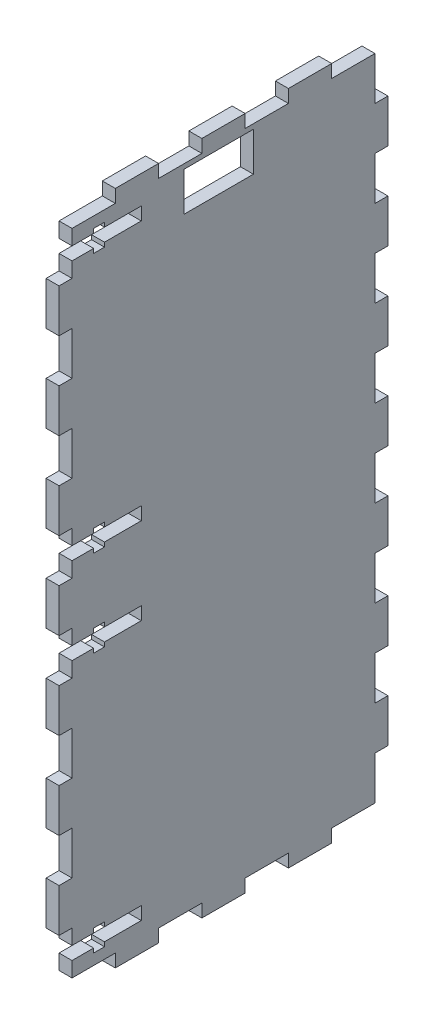
SolidWorks part; units mm, degrees
ref_plane "Front Plane" through (0, 0, 0) normal (0, 0, 1) x (1, 0, 0)
ref_plane "Top Plane" through (0, 0, 0) normal (0, 1, 0) x (1, 0, 0)
ref_plane "Right Plane" through (0, 0, 0) normal (1, 0, 0) x (0, 0, -1)
sketch "Sketch1" plane through (0, 0, 0) normal (1, 0, 0) x (0, 0, -1)
  line L0 (41.909, 148.8936) -> (25.909, 148.8936)
  line L1 (10, 153.0059) -> (20, 153.0059)
  line L2 (0, 140) -> (0, 143.5)
  line L3 (0, 150.0059) -> (10, 150.0059)
  line L4 (10, 150.0059) -> (10, 153.0059)
  line L5 (-3, 120) -> (0, 120)
  line L6 (-3, 130) -> (-3, 140)
  line L7 (0, 130) -> (-3, 130)
  line L8 (0, 120) -> (0, 130)
  line L9 (-3, 100) -> (0, 100)
  line L10 (-3, 110) -> (-3, 120)
  line L11 (0, 110) -> (-3, 110)
  line L12 (-3, 140) -> (0, 140)
  line L13 (0, 100) -> (0, 110)
  line L14 (-3, 80) -> (0, 80)
  line L15 (-3, 90) -> (-3, 100)
  line L16 (0, 90) -> (-3, 90)
  line L17 (0, 80) -> (0, 83.5)
  line L18 (-3, 60) -> (0, 60)
  line L19 (-3, 70) -> (-3, 80)
  line L20 (0, 70) -> (-3, 70)
  line L21 (0, 60) -> (0, 63.5)
  line L22 (-3, 40) -> (0, 40)
  line L23 (-3, 50) -> (-3, 60)
  line L24 (0, 50) -> (-3, 50)
  line L25 (0, 40) -> (0, 50)
  line L26 (-3, 20) -> (0, 20)
  line L27 (-3, 30) -> (-3, 40)
  line L28 (0, 30) -> (-3, 30)
  line L29 (0, 20) -> (0, 30)
  line L30 (-3, 10) -> (-3, 20)
  line L31 (20, 153.0059) -> (20, 150.0059)
  line L32 (0, 10) -> (-3, 10)
  line L33 (0, 0) -> (0, 3.5)
  line L34 (20, 150.0059) -> (30, 150.0059)
  line L35 (30, 153.0059) -> (40, 153.0059)
  line L36 (30, 150.0059) -> (30, 153.0059)
  line L37 (40, 153.0059) -> (40, 150.0059)
  line L38 (40, 150.0059) -> (50, 150.0059)
  line L39 (50, 153.0059) -> (60, 153.0059)
  line L40 (50, 150.0059) -> (50, 153.0059)
  line L41 (60, 153.0059) -> (60, 150.0059)
  line L42 (60, 150.0059) -> (70, 150.0059)
  line L43 (41.909, 148.8936) -> (41.909, 139.8936)
  line L44 (41.909, 139.8936) -> (25.909, 139.8936)
  line L45 (25.909, 139.8936) -> (25.909, 148.8936)
  line L46 (0, 10) -> (0, 6.5)
  line L47 (7.5, 6.5) -> (16, 6.5)
  line L48 (16, 3.5) -> (7.5, 3.5)
  line L49 (70, 0) -> (70, 3.5)
  line L50 (70, 10) -> (73, 10)
  line L51 (73, 10) -> (73, 20)
  line L52 (70, 20) -> (70, 30)
  line L53 (70, 30) -> (73, 30)
  line L54 (73, 30) -> (73, 40)
  line L55 (73, 20) -> (70, 20)
  line L56 (70, 40) -> (70, 50)
  line L57 (70, 50) -> (73, 50)
  line L58 (73, 50) -> (73, 60)
  line L59 (73, 40) -> (70, 40)
  line L60 (70, 60) -> (70, 63.5)
  line L61 (70, 70) -> (73, 70)
  line L62 (73, 70) -> (73, 80)
  line L63 (73, 60) -> (70, 60)
  line L64 (70, 80) -> (70, 83.5)
  line L65 (70, 90) -> (73, 90)
  line L66 (73, 90) -> (73, 100)
  line L67 (73, 80) -> (70, 80)
  line L68 (70, 100) -> (70, 110)
  line L69 (73, 140) -> (70, 140)
  line L70 (70, 110) -> (73, 110)
  line L71 (73, 110) -> (73, 120)
  line L72 (73, 100) -> (70, 100)
  line L73 (70, 120) -> (70, 130)
  line L74 (70, 130) -> (73, 130)
  line L75 (73, 130) -> (73, 140)
  line L76 (73, 120) -> (70, 120)
  line L77 (70, 140) -> (70, 143.5)
  line L78 (7.5, 2.5) -> (5, 2.5)
  line L79 (0, 6.5) -> (5, 6.5)
  line L80 (60, 0) -> (70, 0)
  line L81 (60, -3) -> (60, 0)
  line L82 (50, 0) -> (50, -3)
  line L83 (50, -3) -> (60, -3)
  line L84 (40, 0) -> (50, 0)
  line L85 (40, -3) -> (40, 0)
  line L86 (30, 0) -> (30, -3)
  line L87 (30, -3) -> (40, -3)
  line L88 (20, 0) -> (30, 0)
  line L89 (20, -3) -> (20, 0)
  line L90 (10, 0) -> (10, -3)
  line L91 (0, 0) -> (10, 0)
  line L92 (10, -3) -> (20, -3)
  line L93 (16, 6.5) -> (16, 3.5)
  line L94 (7.5, 2.5) -> (7.5, 3.5)
  line L95 (7.5, 7.5) -> (5, 7.5)
  line L96 (5, 2.5) -> (5, 3.5)
  line L97 (5, 6.5) -> (5, 7.5)
  line L98 (7.5, 6.5) -> (7.5, 7.5)
  line L99 (5, 3.5) -> (0, 3.5)
  line L100 (5, 63.5) -> (0, 63.5)
  line L101 (0, 66.5) -> (5, 66.5)
  line L102 (7.5, 66.5) -> (16, 66.5)
  line L103 (16, 63.5) -> (7.5, 63.5)
  line L104 (7.5, 62.5) -> (5, 62.5)
  line L105 (16, 66.5) -> (16, 63.5)
  line L106 (7.5, 62.5) -> (7.5, 63.5)
  line L107 (7.5, 67.5) -> (5, 67.5)
  line L108 (5, 62.5) -> (5, 63.5)
  line L109 (5, 66.5) -> (5, 67.5)
  line L110 (7.5, 66.5) -> (7.5, 67.5)
  line L111 (5, 83.5) -> (0, 83.5)
  line L112 (0, 86.5) -> (5, 86.5)
  line L113 (7.5, 86.5) -> (16, 86.5)
  line L114 (16, 83.5) -> (7.5, 83.5)
  line L115 (7.5, 82.5) -> (5, 82.5)
  line L116 (16, 86.5) -> (16, 83.5)
  line L117 (7.5, 82.5) -> (7.5, 83.5)
  line L118 (7.5, 87.5) -> (5, 87.5)
  line L119 (5, 82.5) -> (5, 83.5)
  line L120 (5, 86.5) -> (5, 87.5)
  line L121 (7.5, 86.5) -> (7.5, 87.5)
  line L122 (7.5, 146.5) -> (16, 146.5)
  line L123 (16, 143.5) -> (7.5, 143.5)
  line L124 (7.5, 142.5) -> (5, 142.5)
  line L125 (16, 146.5) -> (16, 143.5)
  line L126 (7.5, 142.5) -> (7.5, 143.5)
  line L127 (7.5, 147.5) -> (5, 147.5)
  line L128 (5, 142.5) -> (5, 143.5)
  line L129 (5, 146.5) -> (5, 147.5)
  line L130 (7.5, 146.5) -> (7.5, 147.5)
  line L131 (5, 143.5) -> (0, 143.5)
  line L132 (0, 146.5) -> (5, 146.5)
  line L133 (0, 0) -> (70, 0) construction
  line L134 (70, 6.5) -> (70, 10)
  line L135 (70, 3.5) -> (70, 6.5)
  line L136 (70, 63.5) -> (70, 66.5)
  line L137 (70, 83.5) -> (70, 90)
  line L139 (70, 143.5) -> (70, 146.5)
  line L179 (70, 66.5) -> (70, 70)
  line L181 (70, 146.5) -> (70, 150.0059)
  line L182 (0, 146.5) -> (0, 150.0059)
  line L183 (0, 86.5) -> (0, 90)
  line L184 (0, 66.5) -> (0, 70)
  point P49 (8, 5)
  point P94 (8, 5)
  point P99 (8, 65)
  point P109 (8, 65)
  point P118 (8, 85)
  point P123 (8, 85)
  point P133 (8, 145)
  point P138 (8, 145)
  dimension "D1" = 2
  dimension "D2" = 2
  dimension "D3" = 2
extrude "Boss-Extrude1" add sketch "Sketch1" along normal blind 3
